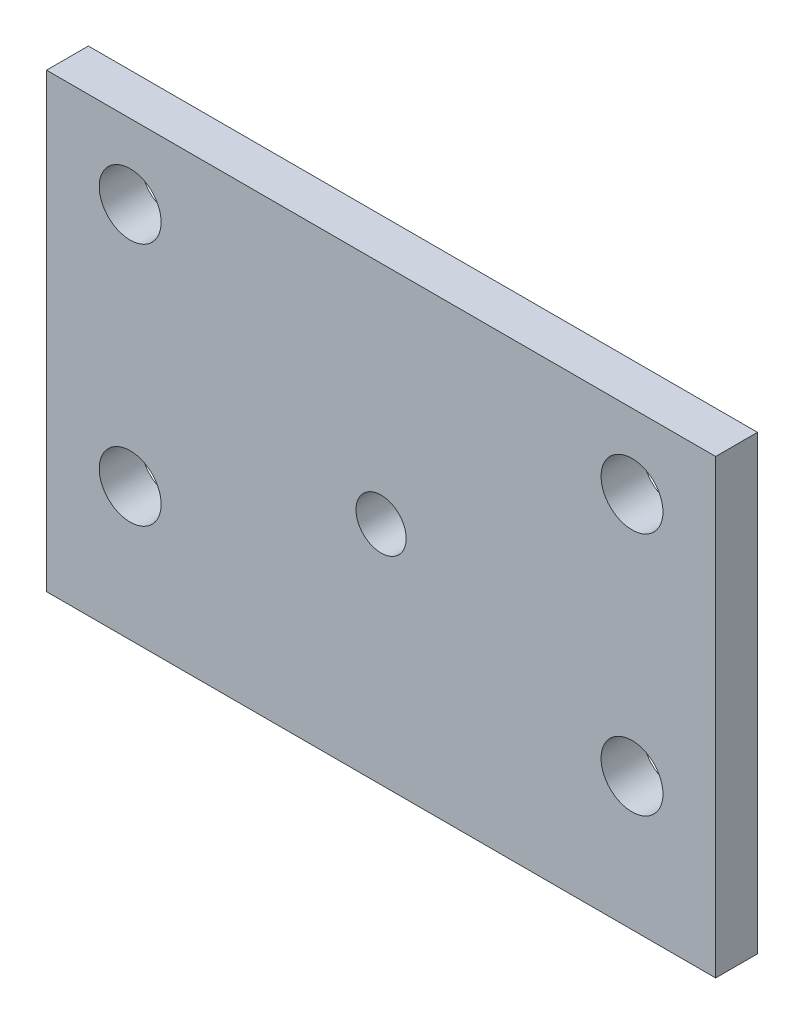
SolidWorks part; units mm, degrees
ref_plane "Front Plane" through (0, 0, 0) normal (0, 0, 1) x (1, 0, 0)
ref_plane "Top Plane" through (0, 0, 0) normal (0, 1, 0) x (1, 0, 0)
ref_plane "Right Plane" through (0, 0, 0) normal (1, 0, 0) x (0, 0, -1)
sketch "Sketch1" plane through (0, 0, 0) normal (0, 0, 1) x (1, 0, 0)
  line L0 (-21.3995, -7.0485) -> (-25.4, -7.0485) construction
  line L1 (-25.4, -17.145) -> (25.4, -17.145)
  line L2 (-25.4, -17.145) -> (-25.4, 17.145)
  line L3 (-25.4, 17.145) -> (25.4, 17.145)
  line L4 (25.4, -17.145) -> (25.4, 17.145)
  line L5 (-25.4, -17.145) -> (25.4, 17.145) construction
  line L6 (-25.4, 17.145) -> (25.4, -17.145) construction
  line L7 (21.3995, -7.0485) -> (25.4, -7.0485) construction
  line L9 (19.05, -7.0485) -> (19.05, -17.145) construction
  circle A0 centre (19.05, -7.0485) radius 2.3495
  circle A1 centre (19.05, 11.4935) radius 2.3495
  circle A2 centre (-19.05, 11.4935) radius 2.3495
  circle A3 centre (-19.05, -7.0485) radius 2.3495
  circle A6 centre (0, 0) radius 1.905
  point P0 (0, 0)
  dimension "D1" = 4.699
  dimension "D2" = 18.542
  dimension "D10" = 3.81
  dimension "D3" = 50.8
  dimension "D4" = 34.29
  dimension "D5" = 4.0005
  dimension "D6" = 10.0965
extrude "Boss-Extrude1" add sketch "Sketch1" along normal blind 3.175
